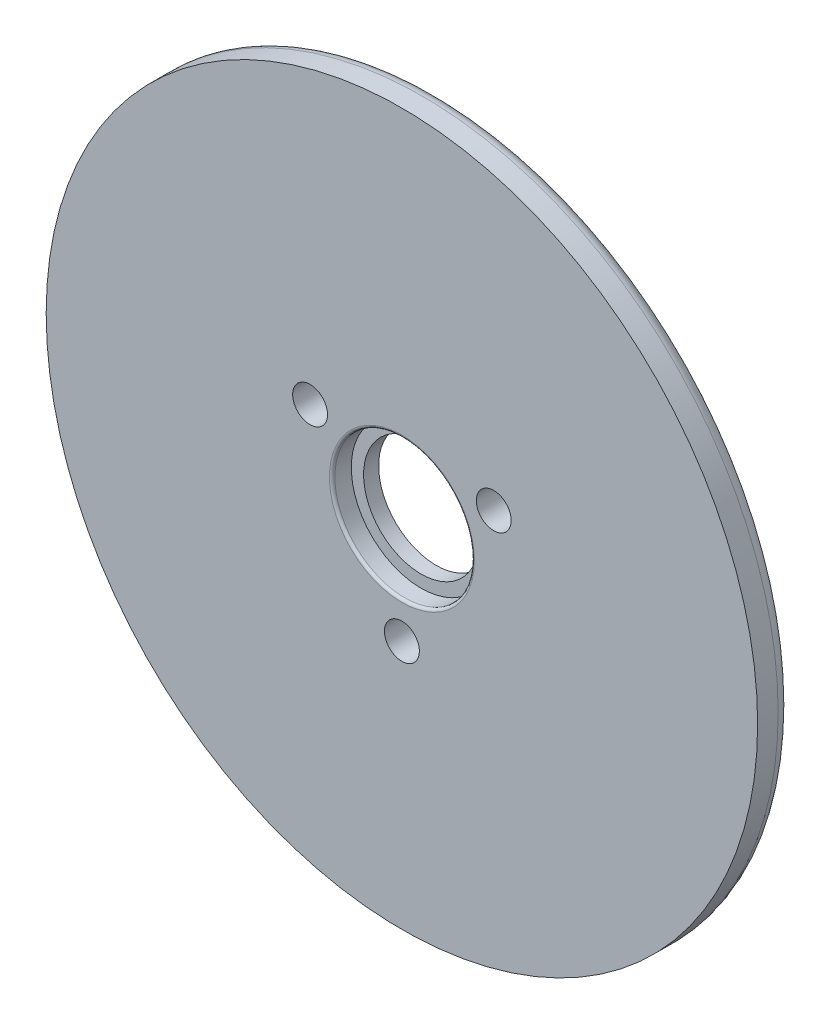
SolidWorks part; units mm, degrees
ref_plane "Front Plane" through (0, 0, 0) normal (0, 0, 1) x (1, 0, 0)
ref_plane "Top Plane" through (0, 0, 0) normal (0, 1, 0) x (1, 0, 0)
ref_plane "Right Plane" through (0, 0, 0) normal (1, 0, 0) x (0, 0, -1)
sketch "Sketch1" plane through (0, 0, 0) normal (0, 0, 1) x (1, 0, 0)
  line L0 (0, 0) -> (0, -7.75) construction
  circle A0 centre (0, 0) radius 4.2
  circle A1 centre (0, 0) radius 26
  circle A2 centre (0, -7.75) radius 1.275
  circle A3 centre (-6.7117, 3.875) radius 1.275
  circle A4 centre (6.7117, 3.875) radius 1.275
  point P12 (0, 0)
  dimension "D3" = 8.4
  dimension "D4" = 2.55
  dimension "D5" = 52
  dimension "D2" = 7.75
  dimension "D1" = 3
extrude "Boss-Extrude1" add sketch "Sketch1" along normal blind 2.5
sketch "Sketch2" plane through (0, 0, 2.5) normal (0, 0, 1) x (1, 0, 0)
  circle A0 centre (0, 0) radius 5.1
  dimension "D1" = 10.2
extrude "Cut-Extrude1" cut sketch "Sketch2" against normal blind 1.4
fillet "Fillet1" radius 0.2 1 edges at (5.1, 0, 2.5)
fillet "Fillet2" radius 1 1 edges at (26, 0, 0)
